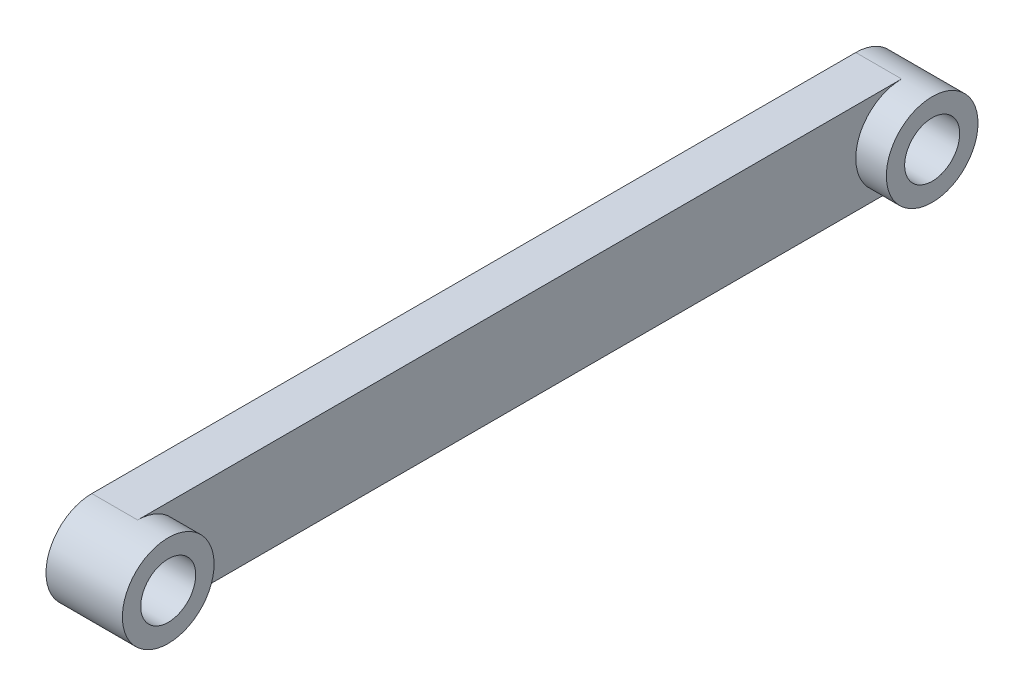
SolidWorks part; units mm, degrees
material "ABS"
ref_plane "Front Plane" through (0, 0, 0) normal (0, 0, 1) x (1, 0, 0)
ref_plane "Top Plane" through (0, 0, 0) normal (0, 1, 0) x (1, 0, 0)
ref_plane "Right Plane" through (0, 0, 0) normal (1, 0, 0) x (0, 0, -1)
sketch "Sketch1" plane through (0, 0, 0) normal (1, 0, 0) x (0, 0, -1)
  line L0 (-66.6033, 3.5627) -> (-16.6033, 3.5627)
  line L1 (-66.6033, 9.5627) -> (-16.6033, 9.5627)
  arc A0 (-66.6033, 9.5627) -> (-66.6033, 3.5627) centre (-66.6033, 6.5627) ccw
  arc A2 (-16.6033, 3.5627) -> (-16.6033, 9.5627) centre (-16.6033, 6.5627) ccw
  circle A3 centre (-66.6033, 6.5627) radius 1.8
  circle A4 centre (-16.6033, 6.5627) radius 1.8
  dimension "D1" = 6
  dimension "D2" = 6
  dimension "D3" = 50
extrude "Boss-Extrude1" add sketch "Sketch1" along normal blind 3
sketch "Sketch2" plane through (3, 0, 0) normal (1, 0, 0) x (0, 0, -1)
  circle A0 centre (-66.6033, 6.5627) radius 3
  circle A1 centre (-66.6033, 6.5627) radius 1.8
  circle A2 centre (-16.6033, 6.5627) radius 1.8
  circle A3 centre (-16.6033, 6.5627) radius 3
extrude "Boss-Extrude2" add sketch "Sketch2" along normal blind 2
